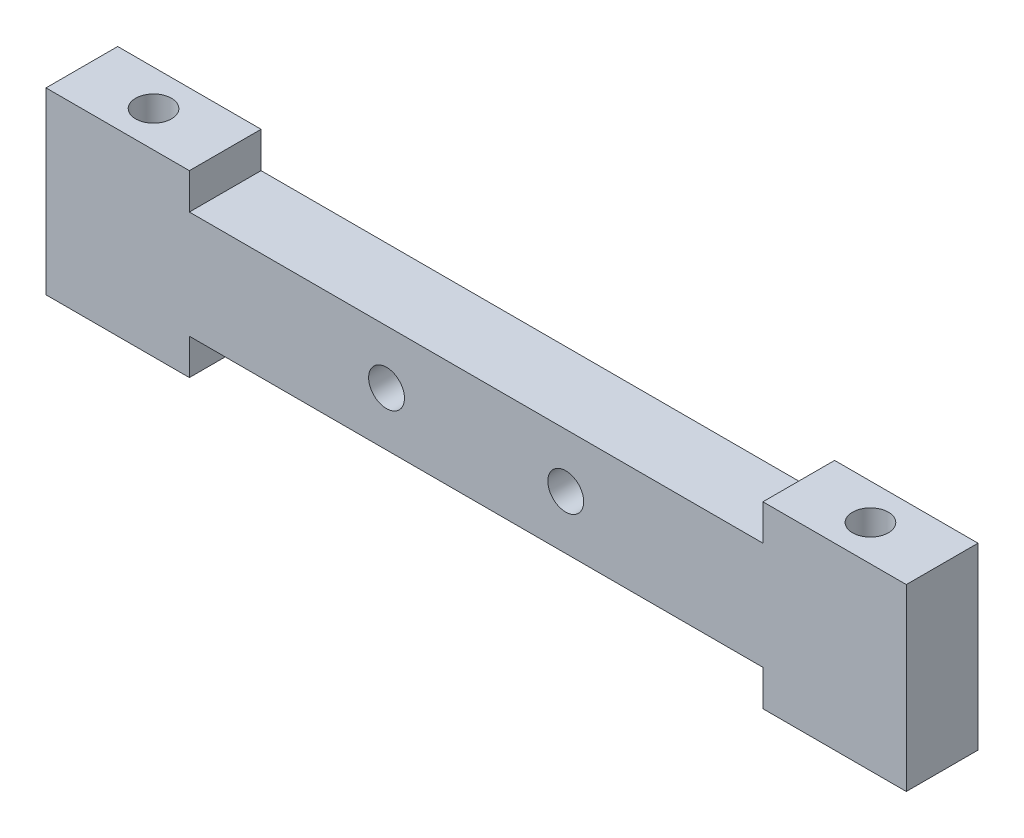
SolidWorks part; units mm, degrees
ref_plane "Plan de face" through (0, 0, 0) normal (0, 0, 1) x (1, 0, 0)
ref_plane "Plan de dessus" through (0, 0, 0) normal (0, 1, 0) x (1, 0, 0)
ref_plane "Plan de droite" through (0, 0, 0) normal (1, 0, 0) x (0, 0, -1)
sketch "Esquisse1" plane through (0, 0, 0) normal (0, 0, 1) x (1, 0, 0)
  line L0 (-99.5377, 33.5408) -> (-99.5377, -64.8283) construction
  line L1 (-119.5377, 25) -> (-79.5377, 25)
  line L2 (-119.5377, 25) -> (-119.5377, -25)
  line L3 (-119.5377, -25) -> (-79.5377, -25)
  line L4 (120.4623, 25) -> (120.4623, -25)
  line L5 (100.4623, 43.3262) -> (100.4623, -64.8283) construction
  line L6 (-79.5377, 25) -> (-79.5377, 15) construction
  line L7 (-79.5377, 15) -> (80.4623, 15) construction
  line L8 (80.4623, 15) -> (80.4623, 25) construction
  line L9 (-79.5377, 25) -> (-79.5377, 15)
  line L10 (-79.5377, 15) -> (80.4623, 15)
  line L11 (80.4623, 15) -> (80.4623, 25)
  line L12 (-119.5377, 0) -> (174.8255, 0) construction
  line L13 (80.4623, -15) -> (80.4623, -25)
  line L14 (-79.5377, -25) -> (-79.5377, -15)
  line L15 (-79.5377, -15) -> (80.4623, -15)
  line L16 (80.4623, 25) -> (120.4623, 25)
  line L17 (80.4623, -25) -> (120.4623, -25)
  line L18 (0.4623, 57.5828) -> (0.4623, -86.6422) construction
  circle A0 centre (-24.5377, 0) radius 5
  circle A1 centre (25.4623, 0) radius 5
  point P19 (25.4623, 0)
  point P20 (-24.5377, 0)
  dimension "D12" = 10
  dimension "D13" = 10
  dimension "D1" = 240
  dimension "D2" = 50
  dimension "D3" = 200
  dimension "D4" = 20
  dimension "D5" = 10
  dimension "D6" = 20
  dimension "D7" = 20
  dimension "D8" = 10
  dimension "D9" = 50
  dimension "D10" = 80
  dimension "D11" = 25
extrude "Boss.-Extru.2" add sketch "Esquisse1" along normal mid plane 20
sketch "Esquisse3" plane through (0, 25, 0) normal (0, 1, 0) x (1, 0, 0)
  line L0 (-119.5377, 0) -> (-79.5377, 0) construction
  line L1 (80.4623, 0) -> (120.4623, 0) construction
  circle A0 centre (-99.5377, 0) radius 5
  circle A1 centre (100.4623, 0) radius 5
extrude "Enlèv. mat.-Extru.1" cut sketch "Esquisse3" against normal through all
